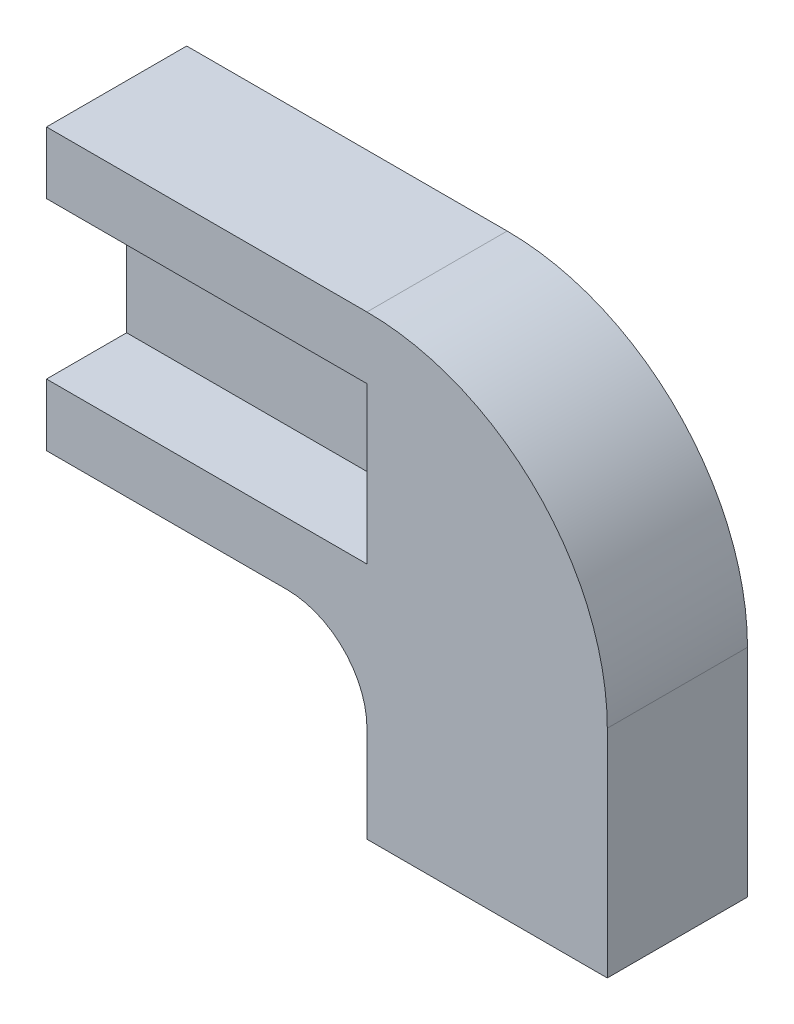
SolidWorks part; units mm, degrees
ref_plane "Front Plane" through (0, 0, 0) normal (0, 0, 1) x (1, 0, 0)
ref_plane "Top Plane" through (0, 0, 0) normal (0, 1, 0) x (1, 0, 0)
ref_plane "Right Plane" through (0, 0, 0) normal (1, 0, 0) x (0, 0, -1)
sketch "Sketch1" plane through (0, 0, 0) normal (0, 0, 1) x (1, 0, 0)
  line L0 (0, 0) -> (17.78, 0)
  line L1 (17.78, 0) -> (17.78, -14.478)
  line L2 (17.78, -14.478) -> (10.16, -14.478)
  line L3 (10.16, -14.478) -> (10.16, -8.89)
  line L4 (10.16, -8.89) -> (0, -8.89)
  line L5 (0, -8.89) -> (0, 0)
  dimension "D1" = 17.78
  dimension "D2" = 8.89
  dimension "D3" = 7.62
  dimension "D4" = 5.588
extrude "Boss-Extrude1" add sketch "Sketch1" along normal blind 4.445
sketch "Sketch2" plane through (0, 0, 4.445) normal (0, 0, 1) x (1, 0, 0)
  line L0 (0, -4.445) -> (17.78, -4.445) construction
  line L1 (0, 0) -> (0, -8.89) construction
  line L2 (17.78, -14.478) -> (17.78, 0) construction
  line L3 (10.16, -8.89) -> (10.16, -14.478) construction
  line L4 (10.16, -1.9685) -> (0, -1.9685)
  line L5 (10.16, -1.9685) -> (10.16, -6.9215)
  line L6 (10.16, -6.9215) -> (0, -6.9215)
  line L7 (0, -1.9685) -> (0, -6.9215)
  line L8 (10.16, -1.9685) -> (0, -6.9215) construction
  line L9 (10.16, -6.9215) -> (0, -1.9685) construction
  line L10 (10.16, -14.478) -> (17.78, -14.478) construction
  point P6 (5.08, -4.445)
  dimension "D1" = 4.953
  dimension "D2" = 12.5095
extrude "Cut-Extrude1" cut sketch "Sketch2" against normal blind 2.54
fillet "Fillet1" radius 2.54 1 edges at (10.16, -8.89, 2.2225)
fillet "Fillet2" radius 7.62 1 edges at (17.78, 0, 2.2225)
